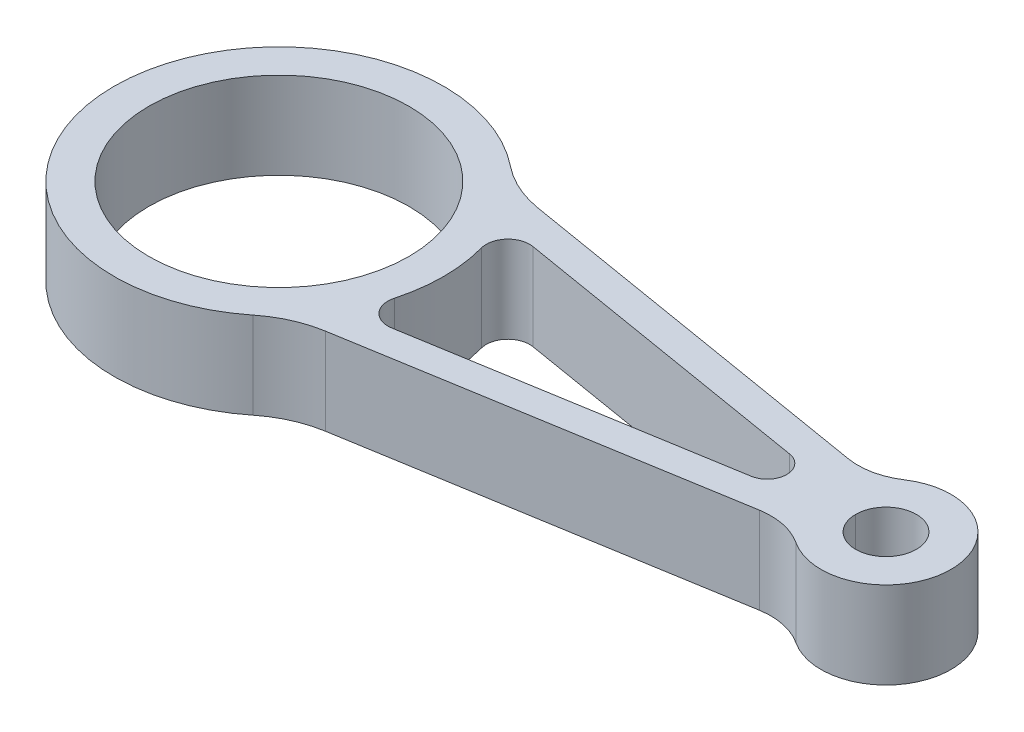
SolidWorks part; units mm, degrees
material "Plain Carbon Steel"
ref_plane "Front Plane" through (0, 0, 0) normal (0, 0, 1) x (1, 0, 0)
ref_plane "Top Plane" through (0, 0, 0) normal (0, 1, 0) x (1, 0, 0)
ref_plane "Right Plane" through (0, 0, 0) normal (1, 0, 0) x (0, 0, -1)
sketch "Sketch1" plane through (0, 0, 0) normal (0, 1, 0) x (1, 0, 0)
  line L0 (0, 0) -> (351.671, 0) construction
  line L1 (135.1294, -5.0277) -> (144.8706, 5.0277) construction
  line L2 (151.416, -9.7301) -> (128.584, 9.7301) construction
  line L3 (-17.2488, -24.5454) -> (17.2488, 24.5454) construction
  line L4 (19.2346, -32.7724) -> (-19.2346, 32.7724) construction
  line L5 (27.9355, 25.7606) -> (128.0638, 9.0844)
  line L6 (27.9355, -25.7606) -> (128.0638, -9.0844)
  circle A0 centre (0, 0) radius 30
  arc A1 (27.9355, 25.7606) -> (27.9355, -25.7606) centre (0, 0) ccw
  circle A3 centre (140, 0) radius 7
  arc A4 (128.0638, 9.0844) -> (128.0638, -9.0844) centre (140, 0) cw
  dimension "D2" = 14
  dimension "D1" = 140
  dimension "D3" = 30
  dimension "D4" = 60
  dimension "D5" = 76
extrude "Boss-Extrude1" add sketch "Sketch1" along normal mid plane 20
fillet "Fillet1" radius 15 2 edges at (128.0638, 0, -9.0844) (128.0638, 0, 9.0844)
fillet "Fillet2" radius 25 2 edges at (27.9355, 0, 25.7606) (27.9355, 0, -25.7606)
sketch "Sketch2" plane through (0, -10, 0) normal (0, -1, 0) x (1, 0, 0)
  line L0 (-1.3707, 0) -> (178.7751, 0) construction
  line L1 (42.2992, 16.2719) -> (113.348, 4.4389)
  line L2 (42.2992, -16.2719) -> (113.348, -4.4389)
  line L3 (35.2357, 24.5448) -> (121.031, 10.2557) construction
  line L5 (121.031, -10.2557) -> (35.2357, -24.5448) construction
  arc A0 (113.348, 4.4389) -> (113.348, -4.4389) centre (112.6087, 0) cw
  arc A1 (36.6548, 10.0213) -> (42.2992, 16.2719) centre (41.4778, 11.3399) cw
  arc A2 (36.6548, 10.0213) -> (36.6548, -10.0213) centre (0, 0) cw
  circle A3 centre (0, 0) radius 30 construction
  arc A4 (36.6548, -10.0213) -> (42.2992, -16.2719) centre (41.4778, -11.3399) ccw
  point P15 (0, 0)
  point P18 (123.6577, 4.2424)
  point P19 (122.9975, 0)
  point P22 (0, 0)
  point P23 (0, 0)
  point P24 (0, 0)
  dimension "D1" = 4.5
  dimension "D2" = 5
  dimension "D3" = 8
  dimension "D4" = 7
  dimension "D5" = 7
extrude "Cut-Extrude1" cut sketch "Sketch2" against normal through all
mirror "Mirror1" [suppressed] about plane through (0, 0, 0) normal (0, 1, 0)
split line "Split Line2"
